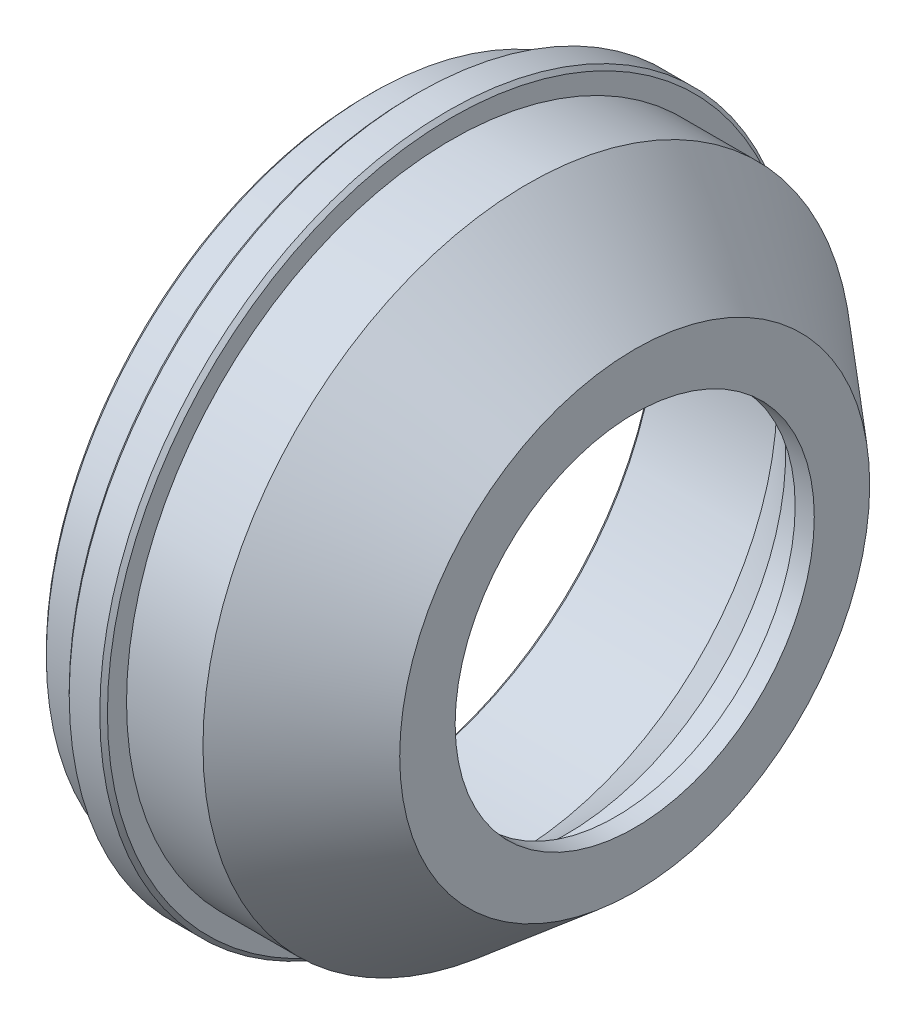
SolidWorks part; units mm, degrees
material "16NiCr4"
ref_plane "Płaszczyzna przednia" through (0, 0, 0) normal (0, 0, 1) x (1, 0, 0)
ref_plane "Płaszczyzna górna" through (0, 0, 0) normal (0, 1, 0) x (1, 0, 0)
ref_plane "Płaszczyzna prawa" through (0, 0, 0) normal (1, 0, 0) x (0, 0, -1)
sketch "Szkic1" plane through (0, 0, 0) normal (0, 0, 1) x (1, 0, 0)
  line L0 (0, 0) -> (116.0172, 0) construction
  line L1 (70, 47) -> (65, 47)
  line L2 (65, 47) -> (65, 57.5)
  line L3 (65, 57.5) -> (52, 57.5)
  line L4 (52, 57.5) -> (38, 69.2474)
  line L5 (38, 69.2474) -> (38, 75)
  line L6 (38, 75) -> (0, 75)
  line L7 (0, 75) -> (0, 85)
  line L8 (0, 85) -> (12, 85)
  line L9 (12, 85) -> (12, 91)
  line L10 (12, 91) -> (22, 91)
  line L11 (22, 91) -> (22, 85)
  line L12 (22, 85) -> (42, 85)
  line L13 (42, 85) -> (70, 61.5052)
  line L14 (70, 61.5052) -> (70, 47)
  dimension "D1" = 94
  dimension "D2" = 115
  dimension "D3" = 150
  dimension "D4" = 38
  dimension "D5" = 12
  dimension "D6" = 10
  dimension "D7" = 6
  dimension "D8" = 170
  dimension "D9" = 5
  dimension "D10" = 13
  dimension "D11" = 70
  dimension "D12" = 40
  dimension "D13" = 40
  dimension "D14" = 20
revolve "Obrót1" add sketch "Szkic1" angle 360 about L0
fillet "Zaokrąglenie1" radius 1 1 edges at (65, 0, 57.5)
fillet "Zaokrąglenie2" radius 1 1 edges at (38, 0, 75)
chamfer "Sfazowanie1" distance 1 angle 45 4 edges at (22, 0, 91) (12, 0, 91) (0, 0, 75) (0, 0, 85)
